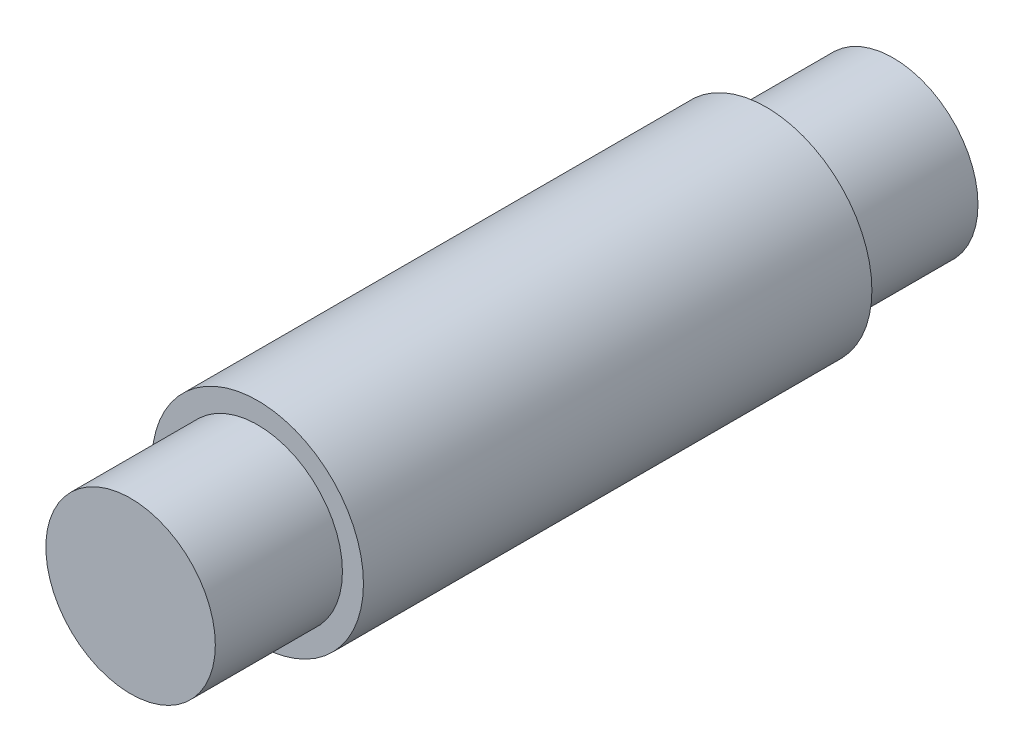
SolidWorks part; units mm, degrees
ref_plane "Front Plane" through (0, 0, 0) normal (0, 0, 1) x (1, 0, 0)
ref_plane "Top Plane" through (0, 0, 0) normal (0, 1, 0) x (1, 0, 0)
ref_plane "Right Plane" through (0, 0, 0) normal (1, 0, 0) x (0, 0, -1)
sketch "Sketch1" plane through (0, 0, 0) normal (0, 0, 1) x (1, 0, 0)
  circle A0 centre (0, 0) radius 3.9624
  dimension "D1" = 7.9248
extrude "Boss-Extrude1" add sketch "Sketch1" along normal mid plane 19.05
sketch "Sketch2" plane through (0, 0, 0) normal (0, 0, 1) x (1, 0, 0)
  circle A0 centre (0, 0) radius 3.175
  dimension "D1" = 6.35
extrude "Boss-Extrude2" add sketch "Sketch2" along normal mid plane 28.575
